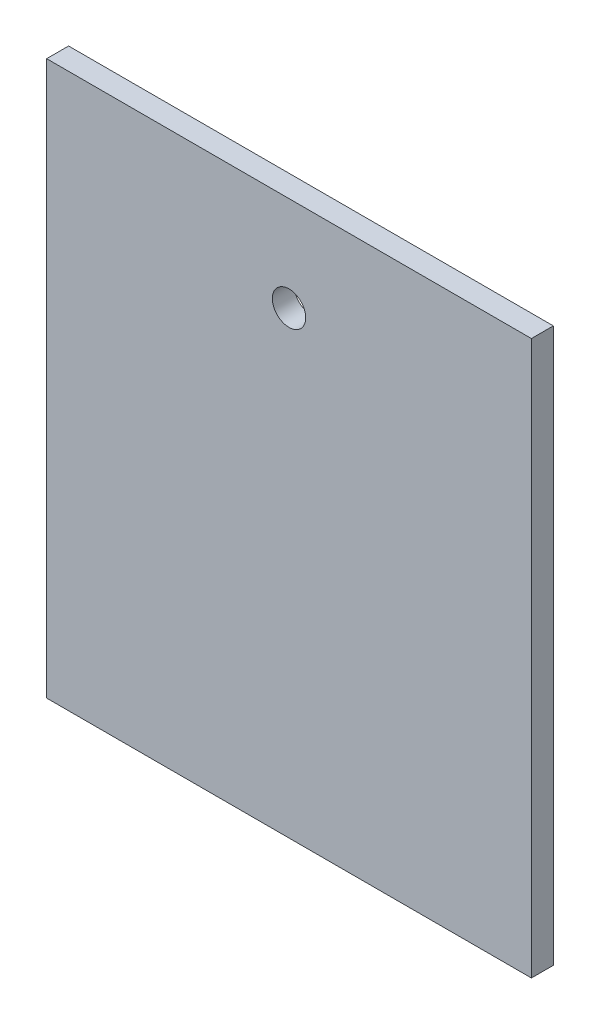
SolidWorks part; units mm, degrees
material "Maple"
ref_plane "Front Plane" through (0, 0, 0) normal (0, 0, 1) x (1, 0, 0)
ref_plane "Top Plane" through (0, 0, 0) normal (0, 1, 0) x (1, 0, 0)
ref_plane "Right Plane" through (0, 0, 0) normal (1, 0, 0) x (0, 0, -1)
sketch "Sketch1" plane through (0, 0, 0) normal (0, 0, 1) x (1, 0, 0)
  line L26 (-33.0336, -0.0826) -> (-33.0336, 80.0833)
  line L27 (-33.0336, 80.0833) -> (37.1356, 80.0833)
  line L28 (37.1356, 80.0833) -> (37.1356, -0.0826)
  line L29 (37.1356, -0.0826) -> (-33.0336, -0.0826)
  circle A0 centre (2.0502, 66.35) radius 2.415
  dimension "D5" = 4.83
  dimension "D1" = 70.1692
  dimension "D2" = 80.1659
  dimension "D3" = 66.4326
extrude "Boss-Extrude1" add sketch "Sketch1" along normal blind 3.175
equation "\"length\"=70"
equation "\"upperlength\"=50"
equation "\"height\"=9"
equation "\"axleDiameter\"=4.83"
equation "\"D5@Sketch1\"=\"axleDiameter\""
equation "\"heightStand\"=80"
equation "\"axleHoleHeight\"=66.35"
